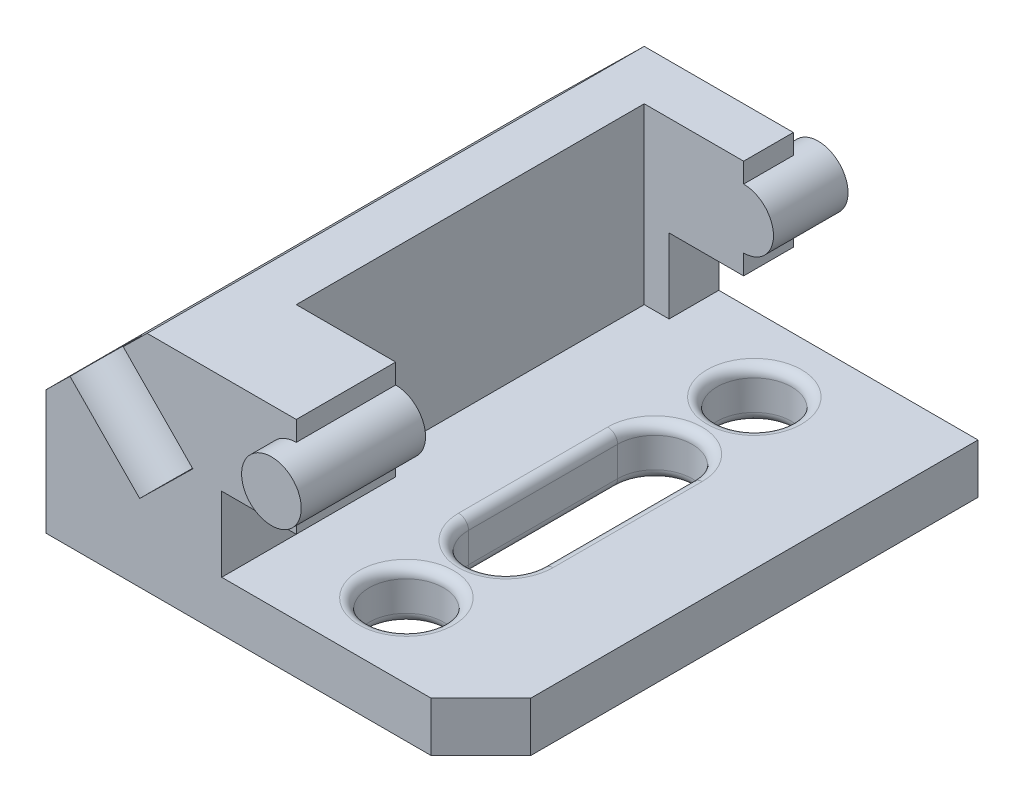
SolidWorks part; units mm, degrees
material "1060 Alloy"
ref_plane "Front Plane" through (0, 0, 0) normal (0, 0, 1) x (1, 0, 0)
ref_plane "Top Plane" through (0, 0, 0) normal (0, 1, 0) x (1, 0, 0)
ref_plane "Right Plane" through (0, 0, 0) normal (1, 0, 0) x (0, 0, -1)
sketch "Sketch1" plane through (0, 0, 0) normal (0, 0, 1) x (1, 0, 0)
  line L0 (-87.5, 0) -> (0, 0)
  line L1 (-87.5, 0) -> (-87.5, 25)
  line L2 (-87.5, 25) -> (-67.1479, 45)
  line L3 (-67.1479, 45) -> (-37.1479, 45)
  line L4 (-37.1479, 45) -> (-37.1479, 25)
  line L5 (-37.1479, 25) -> (-52.1479, 25)
  line L6 (-52.1479, 25) -> (-52.1479, 10)
  line L7 (-52.1479, 10) -> (0, 10)
  line L8 (0, 10) -> (0, 0)
  dimension "D1" = 87.5
  dimension "D2" = 25
  dimension "D3" = 20
  dimension "D4" = 30
  dimension "D5" = 20
  dimension "D6" = 15
  dimension "D7" = 10
  dimension "D8" = 45.5
extrude "Boss-Extrude1" add sketch "Sketch1" along normal blind 100
sketch "Sketch2" plane through (0, 0, 100) normal (0, 0, 1) x (1, 0, 0)
  line L0 (-37.1479, 25) -> (-37.1479, 45) construction
  circle A0 centre (-37.1479, 35) radius 6
  dimension "D1" = 12
  dimension "D2" = 10
extrude "Boss-Extrude3" add sketch "Sketch2" against normal blind 105 and the other way blind 5
sketch "Sketch3" plane through (0, 45, 0) normal (0, 1, 0) x (1, 0, 0)
  line L7 (-37.1479, 0) -> (-67.1479, 0) construction
  line L8 (-57.1479, -80) -> (-31.1479, -80)
  line L9 (-57.1479, -80) -> (-57.1479, -10)
  line L10 (-57.1479, -10) -> (-31.1479, -10)
  line L11 (-31.1479, -80) -> (-31.1479, -10)
  line L12 (-67.1479, -100) -> (-67.1479, 0) construction
  line L15 (-31.1479, -105) -> (-31.1479, 5) construction
  dimension "D1" = 10
  dimension "D2" = 10
  dimension "D3" = 70
extrude "Cut-Extrude2" cut sketch "Sketch3" against normal up to surface (35 mm away) up to face at (-26.0739, 10, 50)
sketch "Sketch4" plane through (0, 10, 0) normal (0, 1, 0) x (1, 0, 0)
  line L0 (-30, -65) -> (-30, -35) construction
  line L1 (-37.5, -65) -> (-37.5, -35)
  line L2 (-22.5, -65) -> (-22.5, -35)
  line L3 (0, -100) -> (0, 0) construction
  line L4 (0, 0) -> (-52.1479, 0) construction
  line L5 (0, -100) -> (-52.1479, -100) construction
  circle A0 centre (-30, -85) radius 7.5
  circle A1 centre (-30, -15) radius 7.5
  arc A2 (-37.5, -65) -> (-22.5, -65) centre (-30, -65) ccw
  arc A3 (-22.5, -35) -> (-37.5, -35) centre (-30, -35) ccw
  point P6 (-30, -50)
  dimension "D1" = 15
  dimension "D2" = 15
  dimension "D3" = 30
  dimension "D4" = 15
  dimension "D5" = 30
  dimension "D6" = 15
  dimension "D7" = 15
  dimension "D8" = 30
  dimension "D9" = 20
extrude "Cut-Extrude3" cut sketch "Sketch4" against normal up to surface (10 mm away) up to face at (-43.75, 0, 50)
sketch "Sketch5" plane through (-55.4846, 56.4615, 0) normal (-0.7009, 0.7133, 0) x (0.7133, 0.7009, 0)
  line L0 (-38.1195, -100) -> (-23.1195, -100)
  line L2 (-16.3523, -100) -> (-44.8867, -100) construction
  arc A0 (-23.1195, -100) -> (-38.1195, -100) centre (-30.6195, -100) ccw
  dimension "D1" = 15
  dimension "D2" = 15
extrude "Cut-Extrude4" cut sketch "Sketch5" against normal blind 20 contours L0 A0
chamfer "Chamfer1" distance 10 angle 45 1 edges at (0, 5, 100)
fillet "Fillet1" radius 2 12 edges at (-30, 0, 72.5) (-22.5, 0, 50) (-30, 0, 27.5) (-30, 10, 27.5) (-22.5, 10, 50) (-30, 10, 72.5) (-30, 0, 22.5) (-37.5, 0, 50) (-30, 0, 92.5) (-30, 10, 22.5) (-37.5, 10, 50) (-30, 10, 92.5)
equation "\"A\" = 87.5"
equation "\"B\" = 70"
equation "\"C\"= 45.5"
equation "\"D1@Sketch1\"= \"A\""
equation "\"D8@Sketch1\"= \"C\""
equation "\"D3@Sketch3\"=\"B\""
